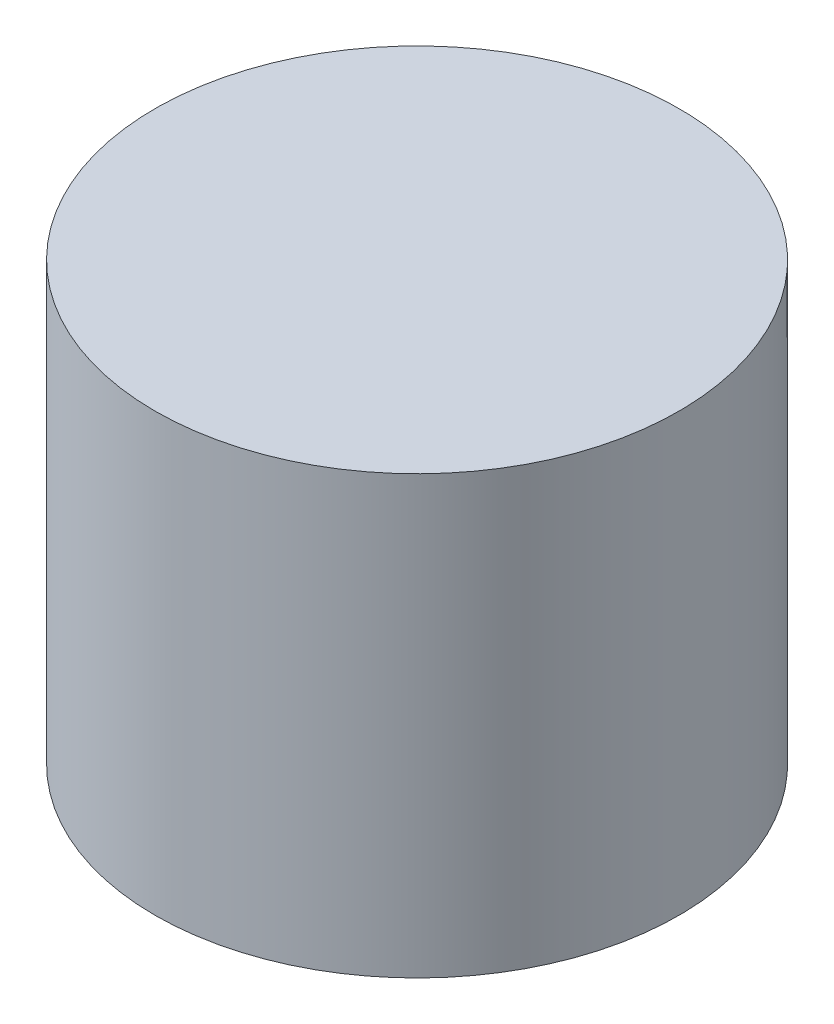
SolidWorks part; units mm, degrees
ref_plane "Front Plane" through (0, 0, 0) normal (0, 0, 1) x (1, 0, 0)
ref_plane "Top Plane" through (0, 0, 0) normal (0, 1, 0) x (1, 0, 0)
ref_plane "Right Plane" through (0, 0, 0) normal (1, 0, 0) x (0, 0, -1)
sketch "Sketch1" plane through (0, 0, 0) normal (0, 1, 0) x (1, 0, 0)
  circle A0 centre (0, 0) radius 1.5
  dimension "D1" = 3
extrude "Boss-Extrude1" add sketch "Sketch1" along normal blind 2.5
